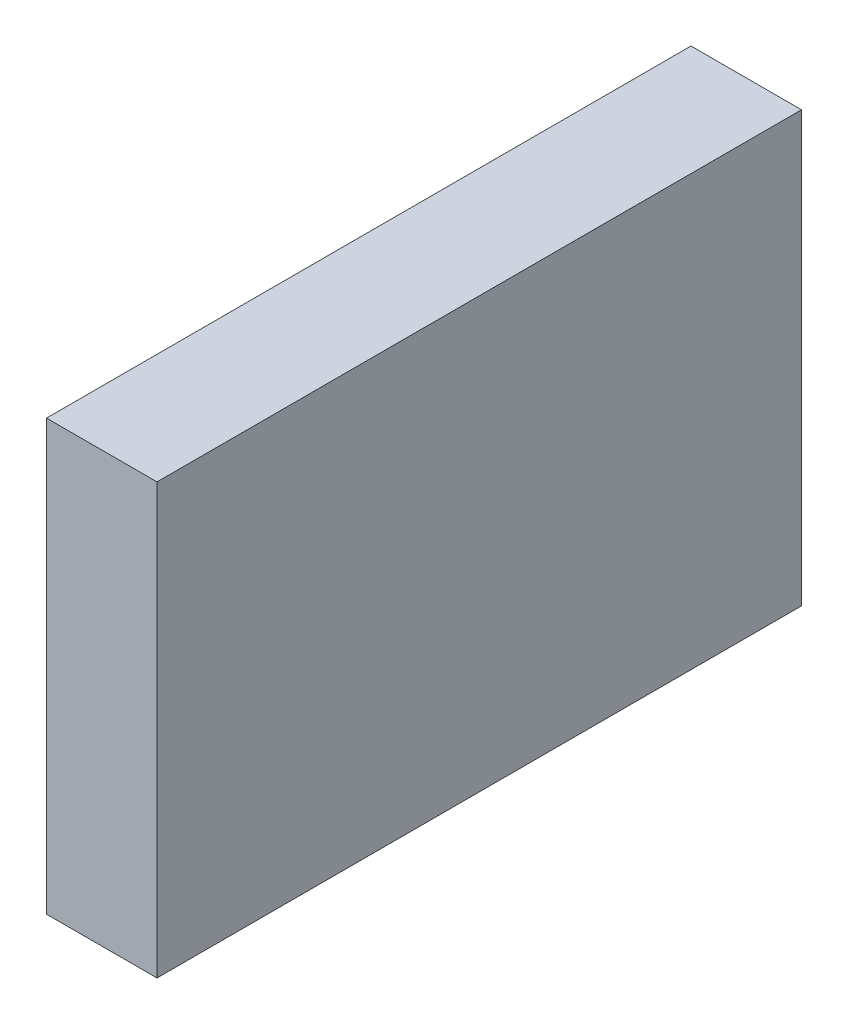
SolidWorks part; units mm, degrees
ref_plane "Front Plane" through (0, 0, 0) normal (0, 0, 1) x (1, 0, 0)
ref_plane "Top Plane" through (0, 0, 0) normal (0, 1, 0) x (1, 0, 0)
ref_plane "Right Plane" through (0, 0, 0) normal (1, 0, 0) x (0, 0, -1)
sketch "Sketch1" plane through (0, 0, 0) normal (0, 1, 0) x (1, 0, 0)
  line L1 (0, 0) -> (3.6, 0)
  line L2 (0, 0) -> (0, 21)
  line L3 (0, 21) -> (3.6, 21)
  line L4 (3.6, 0) -> (3.6, 21)
  dimension "D1" = 3.6
  dimension "D2" = 21
extrude "Boss-Extrude1" add sketch "Sketch1" along normal blind 14
